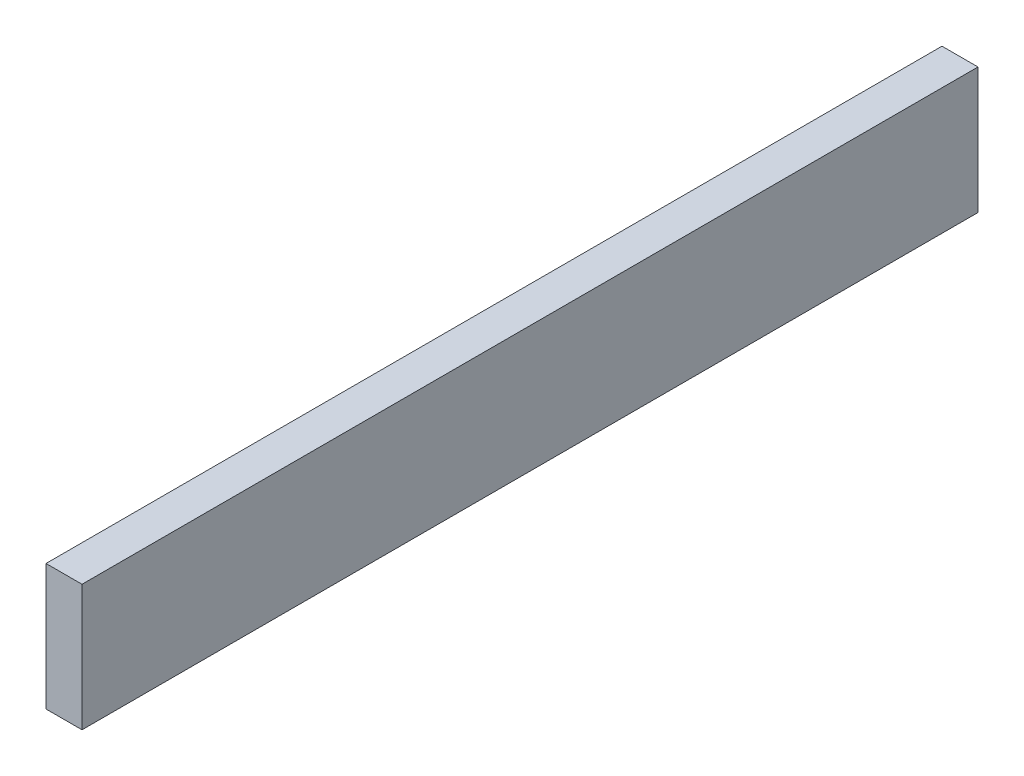
SolidWorks part; units mm, degrees
ref_plane "Front Plane" through (0, 0, 0) normal (0, 0, 1) x (1, 0, 0)
ref_plane "Top Plane" through (0, 0, 0) normal (0, 1, 0) x (1, 0, 0)
ref_plane "Right Plane" through (0, 0, 0) normal (1, 0, 0) x (0, 0, -1)
sketch "Sketch1" plane through (0, 0, 0) normal (1, 0, 0) x (0, 0, -1)
  line L1 (-49.75, 7) -> (49.75, 7)
  line L2 (-49.75, 7) -> (-49.75, -7)
  line L3 (-49.75, -7) -> (49.75, -7)
  line L4 (49.75, 7) -> (49.75, -7)
  line L5 (-49.75, 7) -> (49.75, -7) construction
  line L6 (-49.75, -7) -> (49.75, 7) construction
  point P0 (0, 0)
  dimension "D1" = 99.5
  dimension "D2" = 14
extrude "Boss-Extrude1" add sketch "Sketch1" against normal blind 4
